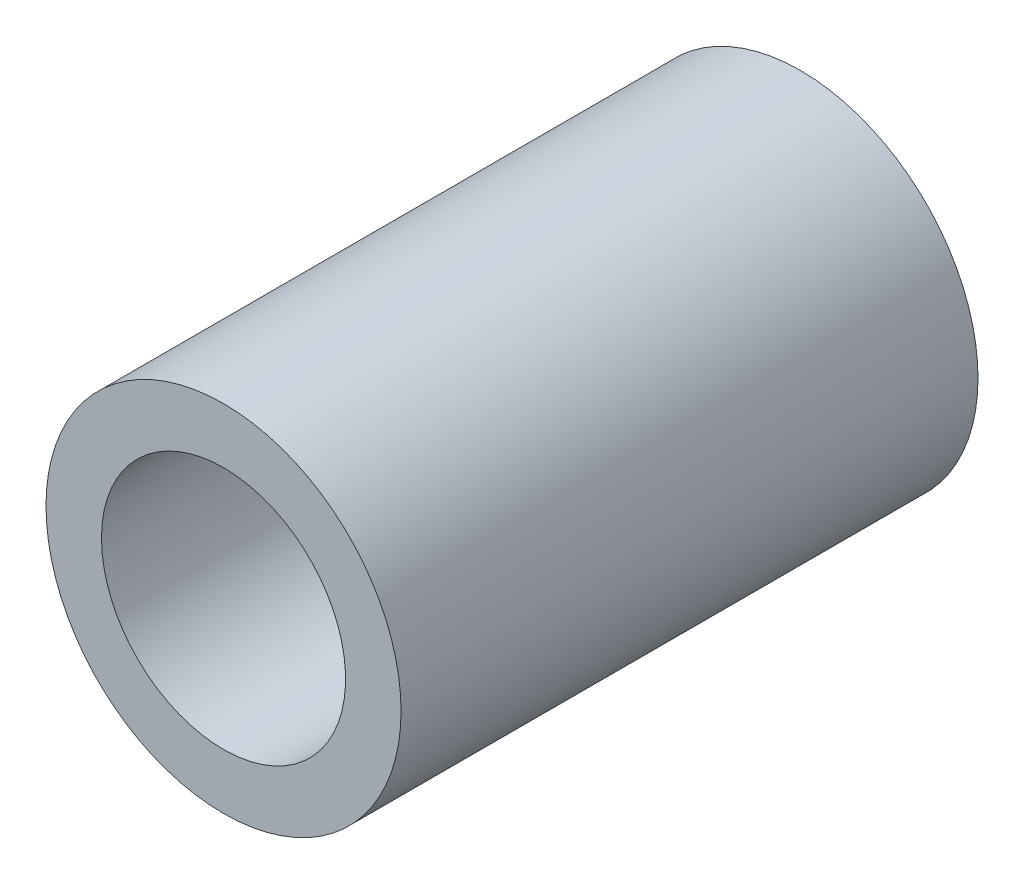
SolidWorks part; units mm, degrees
ref_plane "Front" through (0, 0, 0) normal (0, 0, 1) x (1, 0, 0)
ref_plane "Top" through (0, 0, 0) normal (0, 1, 0) x (1, 0, 0)
ref_plane "Right" through (0, 0, 0) normal (1, 0, 0) x (0, 0, -1)
sketch "Sketch1" plane through (0, 0, 0) normal (0, 0, 1) x (1, 0, 0)
  circle A0 centre (0, 0) radius 16
  dimension "D1" = 32
extrude "Boss-Extrude1" add sketch "Sketch1" along normal blind 52 contours A0
sketch "Sketch2" plane through (0, 0, 0) normal (0, 0, -1) x (-1, 0, 0)
  circle A0 centre (0, 0) radius 11
  dimension "D1" = 22
extrude "Cut-Extrude1" cut sketch "Sketch2" against normal blind 52
